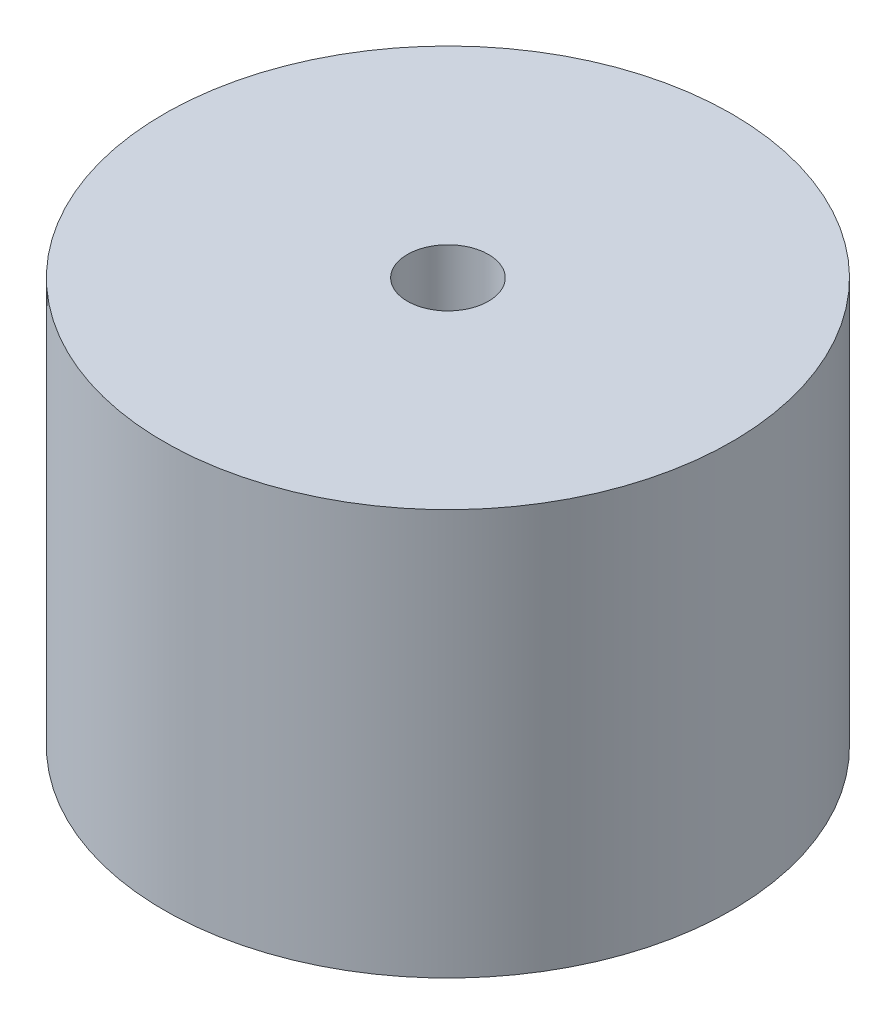
SolidWorks part; units mm, degrees
ref_plane "Front Plane" through (0, 0, 0) normal (0, 0, 1) x (1, 0, 0)
ref_plane "Top Plane" through (0, 0, 0) normal (0, 1, 0) x (1, 0, 0)
ref_plane "Right Plane" through (0, 0, 0) normal (1, 0, 0) x (0, 0, -1)
sketch "Sketch1" plane through (0, 0, 0) normal (0, 0, 1) x (1, 0, 0)
  line L0 (-41.275, 0) -> (-44.45, 0)
  line L1 (-44.45, 0) -> (-44.45, 63.5)
  line L2 (-44.45, 63.5) -> (-6.35, 63.5)
  line L3 (-41.275, 0) -> (-41.275, 60.325)
  line L4 (-41.275, 60.325) -> (-9.525, 60.325)
  line L5 (-9.525, 60.325) -> (-9.525, 38.1)
  line L6 (-9.525, 38.1) -> (-6.35, 38.1)
  line L7 (-6.35, 38.1) -> (-6.35, 63.5)
  line L8 (0, 0) -> (0, 33.9375) construction
  dimension "D1" = 41.275
  dimension "D2" = 44.45
  dimension "D3" = 6.35
  dimension "D4" = 3.175
  dimension "D5" = 3.175
  dimension "D6" = 63.5
  dimension "D7" = 25.4
revolve "Revolve1" add sketch "Sketch1" angle 360 about L8
